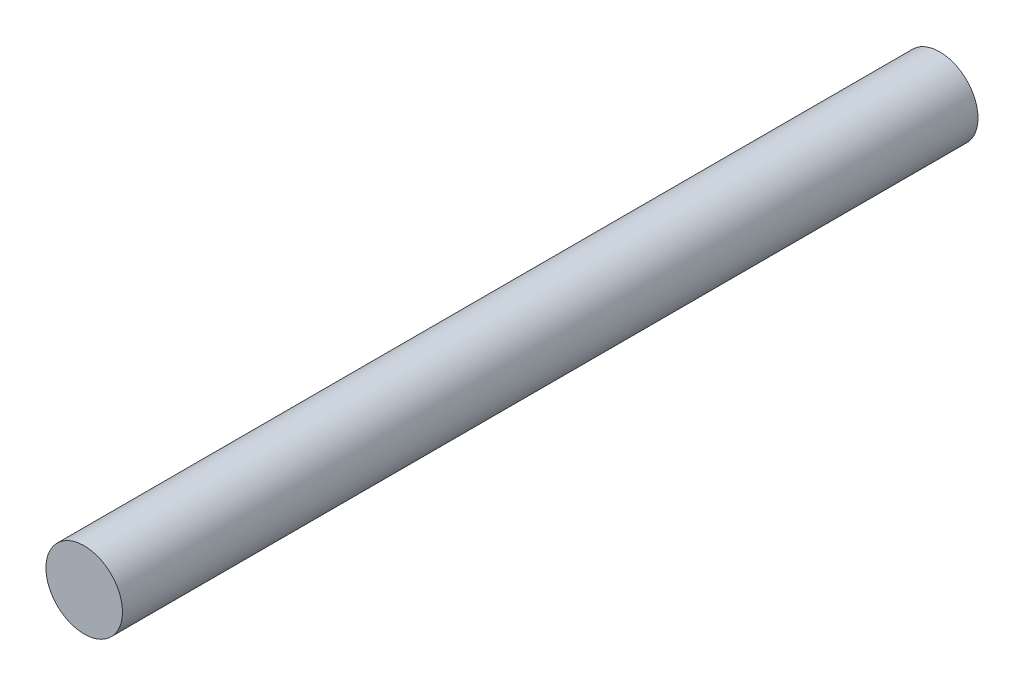
SolidWorks part; units mm, degrees
material "AISI 304"
ref_plane "前视基准面" through (0, 0, 0) normal (0, 0, 1) x (1, 0, 0)
ref_plane "上视基准面" through (0, 0, 0) normal (0, 1, 0) x (1, 0, 0)
ref_plane "右视基准面" through (0, 0, 0) normal (1, 0, 0) x (0, 0, -1)
other "Configuration Table"
sketch "草图1" plane through (0, 0, 0) normal (0, 0, 1) x (1, 0, 0)
  line L0 (0, 0) -> (-6.2607, 0) construction
  line L1 (0, 0) -> (6.2607, 0) construction
  circle A0 centre (0, 0) radius 6.2607
  dimension "D1" = 12.5213
extrude "凸台-拉伸1" add sketch "草图1" along normal blind 140
